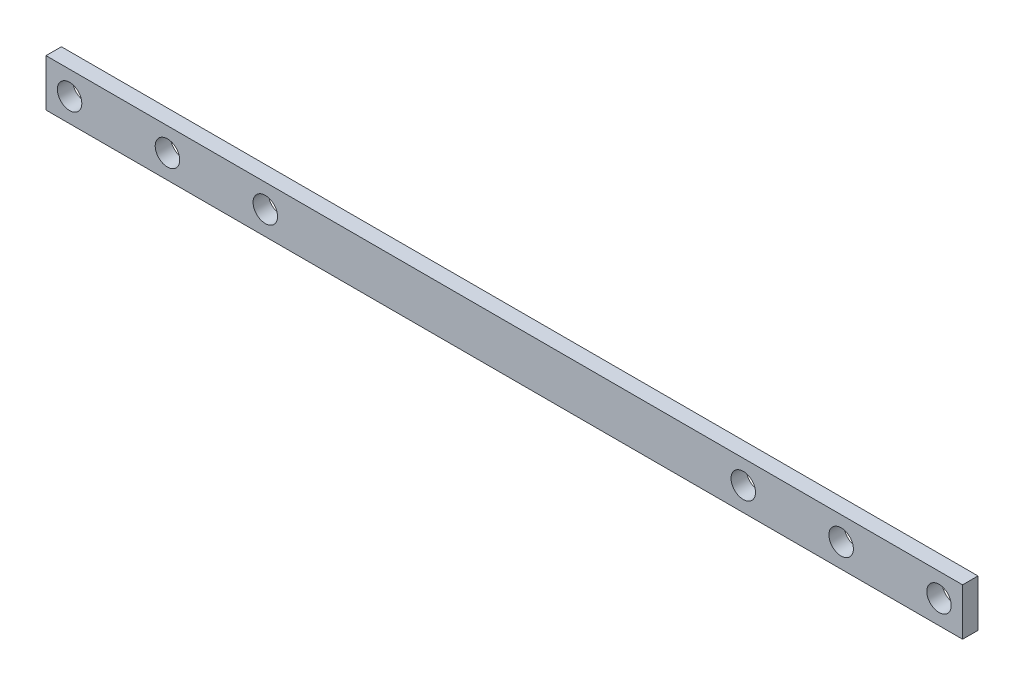
SolidWorks part; units mm, degrees
ref_plane "Front Plane" through (0, 0, 0) normal (0, 0, 1) x (1, 0, 0)
ref_plane "Top Plane" through (0, 0, 0) normal (0, 1, 0) x (1, 0, 0)
ref_plane "Right Plane" through (0, 0, 0) normal (1, 0, 0) x (0, 0, -1)
sketch "Sketch2" plane through (0, 0, 0) normal (0, 0, 1) x (1, 0, 0)
  line L0 (-149.4725, 36.2313) -> (-30.5275, 36.2313)
  line L1 (-30.5275, 36.2313) -> (-30.5275, 30.1113)
  line L2 (-30.5275, 30.1113) -> (-149.4725, 30.1113)
  line L3 (-149.4725, 30.1113) -> (-149.4725, 36.2313)
  circle A0 centre (-146.4125, 33.175) radius 1.5875
  circle A1 centre (-133.7125, 33.175) radius 1.5875
  circle A2 centre (-121.0125, 33.175) radius 1.5875
  circle A3 centre (-58.9875, 33.175) radius 1.5875
  circle A4 centre (-46.2875, 33.175) radius 1.5875
  circle A5 centre (-33.5875, 33.175) radius 1.5875
extrude "Boss-Extrude1" add sketch "Sketch2" along normal blind 2
